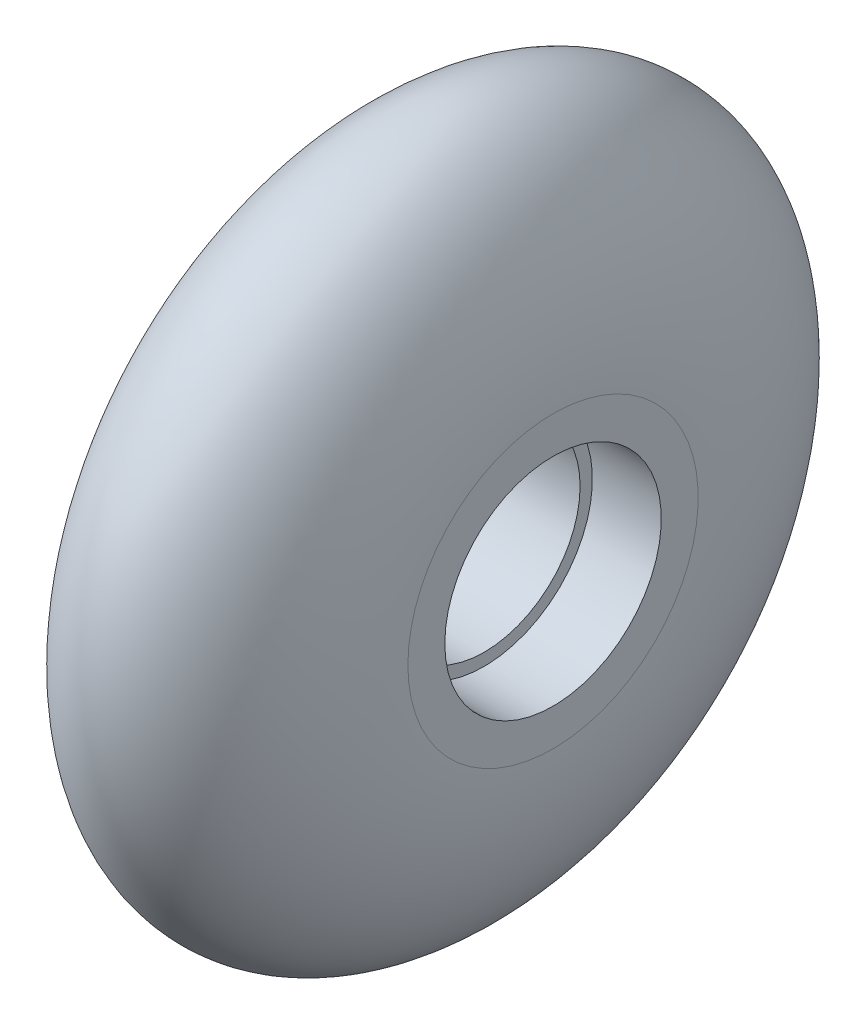
SolidWorks part; units mm, degrees
ref_plane "Front Plane" through (0, 0, 0) normal (0, 0, 1) x (1, 0, 0)
ref_plane "Top Plane" through (0, 0, 0) normal (0, 1, 0) x (1, 0, 0)
ref_plane "Right Plane" through (0, 0, 0) normal (1, 0, 0) x (0, 0, -1)
sketch "Sketch1" plane through (0, 0, 0) normal (0, 0, 1) x (1, 0, 0)
  line L0 (0, 9.75) -> (0, 14.75)
  line L1 (0, 9.75) -> (24.4, 9.75) construction
  line L2 (24.4, 9.75) -> (24.4, 14.75)
  line L3 (0, 14.75) -> (24.4, 14.75) construction
  line L6 (0, 0) -> (24.4, 0) construction
  line L7 (0, 0) -> (0, 9.75) construction
  line L8 (0, 9.75) -> (24.4, 9.75)
  line L9 (24.4, 0) -> (24.4, 9.75) construction
  ellipse E0 centre (12.2, 14.75) end of major axis (12.2, -6.5) minor radius 12.2 (0, 14.75) -> (24.4, 14.75) cw
  dimension "D1" = 5
  dimension "D2" = 24.4
  dimension "D3" = 36
  dimension "D4" = 9.75
revolve "Revolve1" add sketch "Sketch1" angle 360 about L6
sketch "Sketch2" plane through (0, 0, 0) normal (-1, 0, 0) x (0, 0, 1)
  circle A0 centre (0, 0) radius 11
  dimension "D1" = 22
extrude "Cut-Extrude1" cut sketch "Sketch2" against normal blind 7
ref_plane "Plane1" through (12.2, 0, 0) normal (-1, 0, 0) x (0, 0, 1)
mirror "Mirror1" about plane through (12.2, 0, 0) normal (-1, 0, 0) of "Cut-Extrude1"
